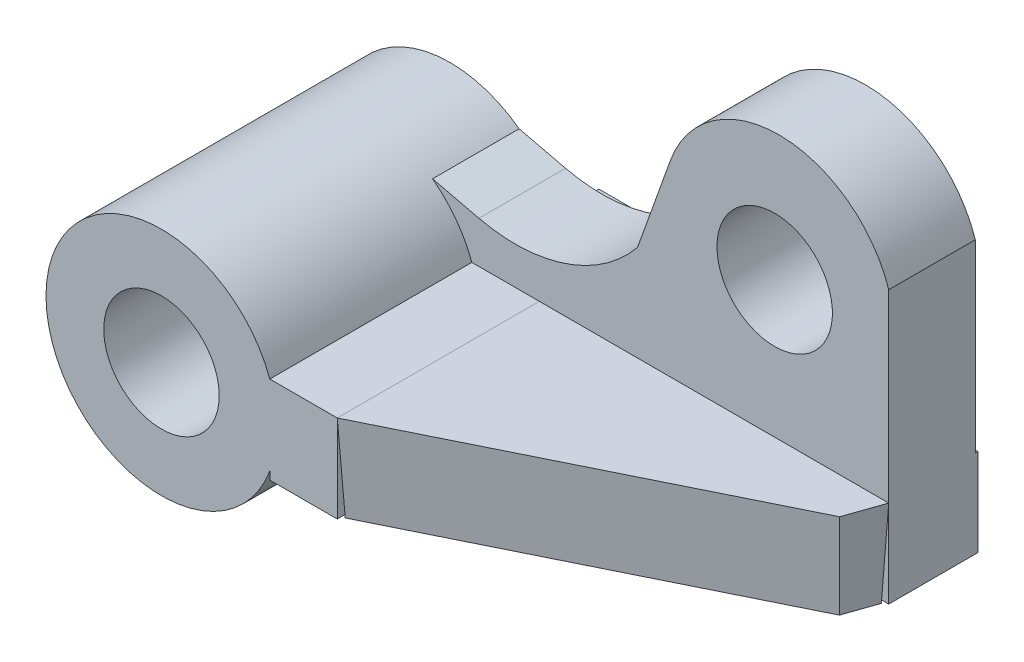
SolidWorks part; units mm, degrees
ref_plane "Front Plane" through (0, 0, 0) normal (0, 0, 1) x (1, 0, 0)
ref_plane "Top Plane" through (0, 0, 0) normal (0, 1, 0) x (1, 0, 0)
ref_plane "Right Plane" through (0, 0, 0) normal (1, 0, 0) x (0, 0, -1)
sketch "Sketch1" plane through (0, 0, 0) normal (0, 0, 1) x (1, 0, 0)
  circle A0 centre (0, 0) radius 20
  circle A1 centre (0, 0) radius 10
  dimension "D1" = 40
  dimension "D2" = 20
extrude "Boss-Extrude1" add sketch "Sketch1" along normal mid plane 50
sketch "Sketch3" plane through (0, 0, -25) normal (0, 0, -1) x (-1, 0, 0)
  line L0 (-11.9591, 16.0306) -> (-20, 14.13)
  line L1 (-47.4742, 23.5) -> (-53.1598, 39.3768)
  line L2 (-90.983, 38.897) -> (-90.983, 6.897)
  line L3 (-90.983, 6.897) -> (-18.7732, 6.897)
  circle A0 centre (0, 0) radius 20 construction
  arc A1 (-20, 14.13) -> (-47.4742, 23.5) centre (-26.2774, 40.6883) cw
  arc A2 (-53.1598, 39.3768) -> (-90.983, 38.897) centre (-71.9889, 32.6341) ccw
  circle A3 centre (-71.2259, 30.5033) radius 10
  circle M1 centre (0, 0) radius 20
  dimension "D1" = 27.29
  dimension "D3" = 20
  dimension "D4" = 32
  dimension "D2" = 20
extrude "Boss-Extrude2" add sketch "Sketch3" against normal blind 15 contours L1 A2 L2 L3 L0 A1 A3 M1
sketch "Sketch5" plane through (0, 0, 25) normal (0, 0, 1) x (1, 0, 0)
  line L0 (0, 0) -> (20, 0) construction
  line L2 (18.7732, 6.897) -> (30.4592, 6.897)
  line L3 (18.7732, 6.897) -> (18.7732, -8.2638)
  line L4 (18.7732, -8.2638) -> (30.4592, -8.2638)
  line L5 (30.4592, 6.897) -> (30.4592, -8.2638)
  circle A0 centre (0, 0) radius 20 construction
  point P9 (20, 0)
extrude "Boss-Extrude4" add sketch "Sketch5" against normal blind 57
sketch "Sketch8" plane through (0, 6.897, 0) normal (0, 1, 0) x (1, 0, 0)
  line L0 (30.4592, -25) -> (88.7949, 3.6939)
  line L1 (88.7949, 3.6939) -> (90.983, 10)
  line L2 (90.983, 10) -> (30.4592, 10)
  line L3 (30.4592, 10) -> (30.4592, -25)
extrude "Boss-Extrude7" add sketch "Sketch8" against normal up to vertex (15.1607 mm away) draft 2 separate body up to point (30.4592, -8.2638, -32)
sketch "Sketch9" plane through (90.983, 0, 0) normal (1, 0, 0) x (0, 0, -1)
  line L0 (32, -8.2638) -> (-25, -8.2638) construction
  line L1 (10, 6.897) -> (25.4662, 6.897)
  line L2 (10, 6.897) -> (10, -8.2638)
  line L3 (10, -8.2638) -> (25.4662, -8.2638)
  line L4 (25.4662, 6.897) -> (25.4662, -8.2638)
extrude "Boss-Extrude8" add sketch "Sketch9" against normal blind 71
